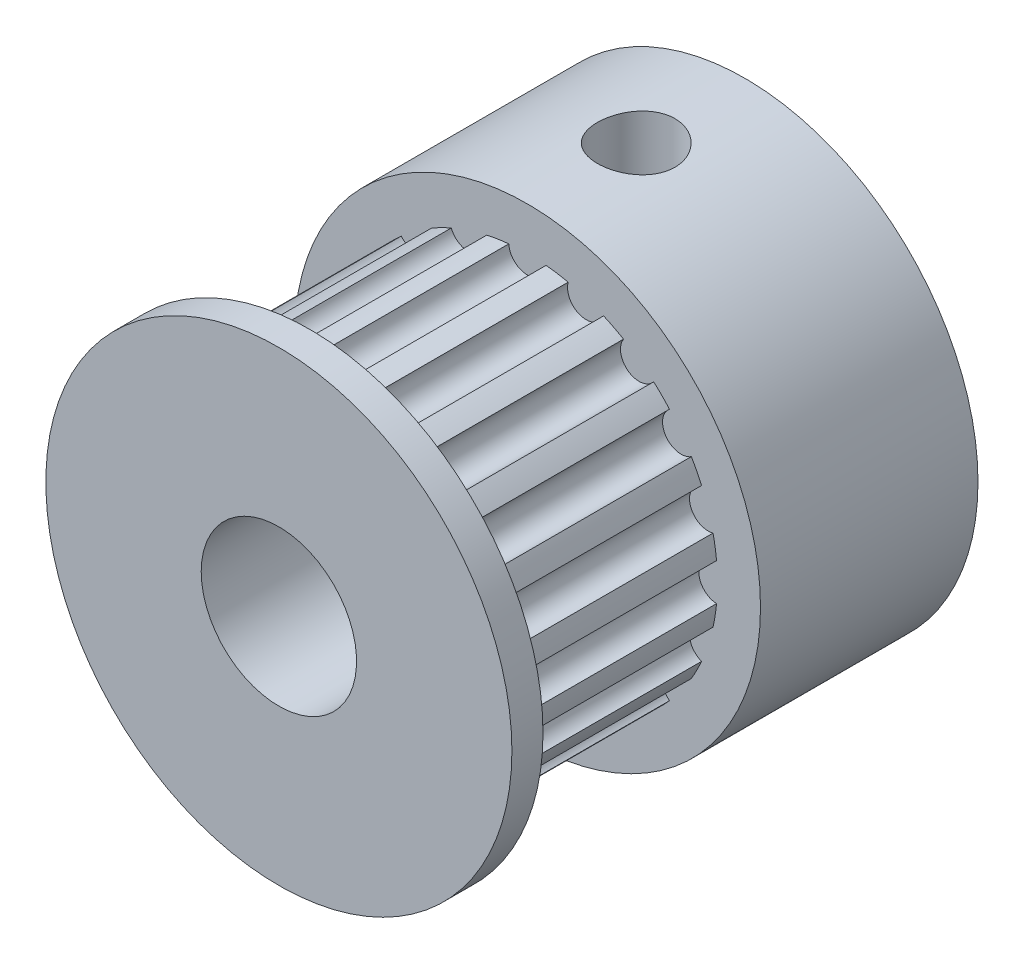
SolidWorks part; units mm, degrees
material "6061 合金"
ref_plane "前基準面" through (0, 0, 0) normal (0, 0, 1) x (1, 0, 0)
ref_plane "上基準面" through (0, 0, 0) normal (0, 1, 0) x (1, 0, 0)
ref_plane "右基準面" through (0, 0, 0) normal (1, 0, 0) x (0, 0, -1)
sketch "草圖1" plane through (0, 0, 0) normal (0, 0, 1) x (1, 0, 0)
  circle A0 centre (0, 0) radius 7.5
  dimension "D1" = 15
extrude "填料-伸長1" add sketch "草圖1" along normal mid plane 7
sketch "草圖2" plane through (0, 0, 3.5) normal (0, 0, 1) x (1, 0, 0)
  circle A0 centre (0, 0) radius 6.115
  dimension "D1" = 12.23
extrude "填料-伸長2" add sketch "草圖2" along normal blind 7
sketch "草圖7" plane through (0, 0, 10.5) normal (0, 0, 1) x (1, 0, 0)
  line L0 (0, 0) -> (0, 6.115) construction
  arc A0 (-0.5993, 6.0856) -> (0.5993, 6.0856) centre (0, 6.115) ccw
  circle A1 centre (0, 0) radius 6.115 construction
  circle A2 centre (0, 0) radius 6.115 construction
  arc A3 (-0.5993, 6.0856) -> (0.5993, 6.0856) centre (0, 0) cw
  point P10 (0, 5.515)
  dimension "D1" = 0.6
extrude "除料-伸長3" cut sketch "草圖7" against normal up to surface (7 mm away) up to face at (6.115, 0, 3.5)
sketch "草圖3" plane through (0, 0, 10.5) normal (0, 0, 1) x (1, 0, 0)
  circle A0 centre (0, 0) radius 7.5
  circle A1 centre (0, 0) radius 7.5 construction
extrude "填料-伸長3" add sketch "草圖3" along normal blind 1
sketch "草圖6" plane through (0, 0, -3.5) normal (0, 0, -1) x (-1, 0, 0)
  circle A0 centre (0, 0) radius 2.5
  dimension "D1" = 5
extrude "除料-伸長2" cut sketch "草圖6" against normal through all
pattern_circular "環狀複製排列2" count 20 over 360 about axis through (0, 0, 0) along (0, 0, 1) of "除料-伸長3"
hole_wizard "M3x0.5 螺紋孔3" positions "草圖12" profile "草圖13" tap size "M3x0.5" standard "Ansi Metric"
sketch "草圖12" plane through (0, 0, 0) normal (0, 1, 0) x (1, 0, 0)
  point P0 (0, 0)
sketch "草圖13" plane through (0, 0, 0) normal (1, 0, 0) x (0, 0, -1)
  line L0 (0, 0) -> (0, 7.5)
  line L1 (0, 7.5) -> (1.25, 7.5)
  line L2 (1.25, 7.5) -> (1.25, 0)
  line L5 (1.25, 0) -> (0, 0)
  line L11 (0, -6.35) -> (0, 107.95) construction
  dimension "貫穿螺孔鑽直徑" = 2.5
  dimension "貫穿螺孔鑽深度" = 7.5
pattern_circular "環狀複製排列4" count 2 over 90 about axis through (0, 0, 3.5) along (0, 0, -1) of "M3x0.5 螺紋孔3"
